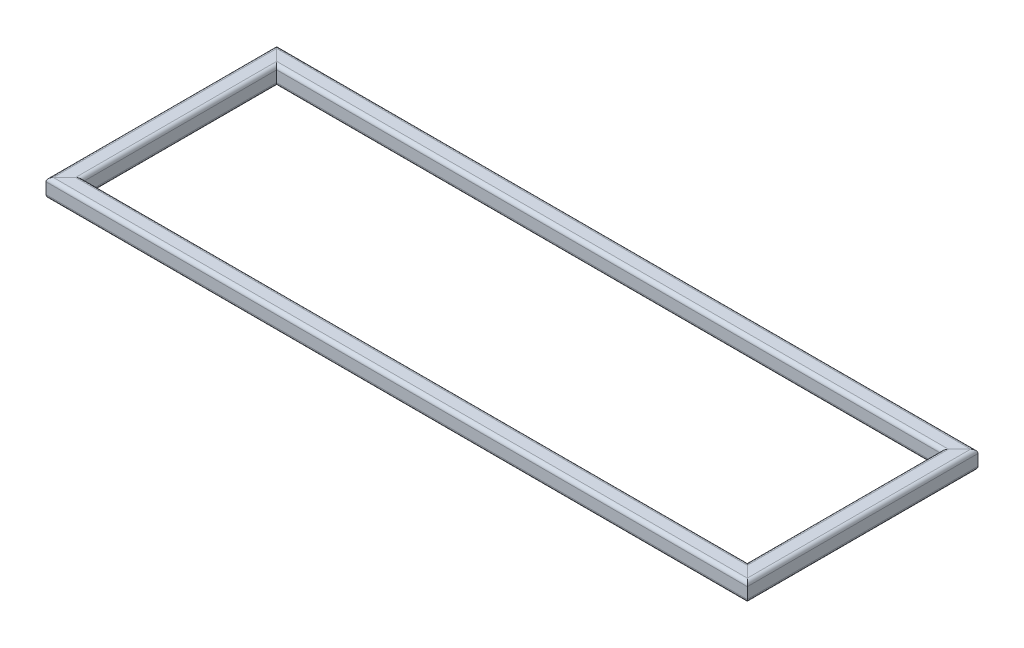
SolidWorks part; units mm, degrees
ref_plane "Front Plane" through (0, 0, 0) normal (0, 0, 1) x (1, 0, 0)
ref_plane "Top Plane" through (0, 0, 0) normal (0, 1, 0) x (1, 0, 0)
ref_plane "Right Plane" through (0, 0, 0) normal (1, 0, 0) x (0, 0, -1)
sketch "Sketch1" plane through (0, 0, 0) normal (0, 1, 0) x (1, 0, 0)
  line L1 (380, -125) -> (-380, -125)
  line L2 (380, -125) -> (380, 125)
  line L3 (380, 125) -> (-380, 125)
  line L4 (-380, -125) -> (-380, 125)
  line L5 (380, -125) -> (-380, 125) construction
  line L6 (380, 125) -> (-380, -125) construction
  point P0 (0, 0)
  dimension "D1" = 250
  dimension "D2" = 760
other "Square tube - configured 20 X 20 X 2(1)"
ref_plane "Plane1" through (380, 0, -115) normal (-1, 0, 0) x (0, 0, 1)
sketch "Sketch11" plane through (380, 0, -115) normal (-1, 0, 0) x (0, 0, 1)
  line L0 (-6, -8) -> (6, -8)
  line L1 (-8, -6) -> (-8, 6)
  line L2 (6, 8) -> (-6, 8)
  line L3 (8, 6) -> (8, -6)
  line L4 (-6, -10) -> (6, -10)
  line L5 (-10, -6) -> (-10, 6)
  line L6 (6, 10) -> (-6, 10)
  line L7 (10, 6) -> (10, -6)
  arc A0 (10, 6) -> (6, 10) centre (6, 6) ccw
  arc A1 (6, -10) -> (10, -6) centre (6, -6) ccw
  arc A2 (-10, -6) -> (-6, -10) centre (-6, -6) ccw
  arc A3 (-6, 10) -> (-10, 6) centre (-6, 6) ccw
  arc A4 (-6, 8) -> (-8, 6) centre (-6, 6) ccw
  arc A5 (8, 6) -> (6, 8) centre (6, 6) ccw
  arc A6 (6, -8) -> (8, -6) centre (6, -6) ccw
  arc A7 (-8, -6) -> (-6, -8) centre (-6, -6) ccw
  point P0 (-10, 0)
  point P1 (10, 0)
  point P2 (0, 10)
  point P3 (0, -10)
  point P4 (0, 0)
  point P5 (-10, -10)
  point P6 (10, -10)
  point P7 (10, 10)
  point P8 (-10, 10)
  point P33 (0, 0)
  dimension "D1" = 4
  dimension "Thickness" = 2
  dimension "V_leg" = 20
